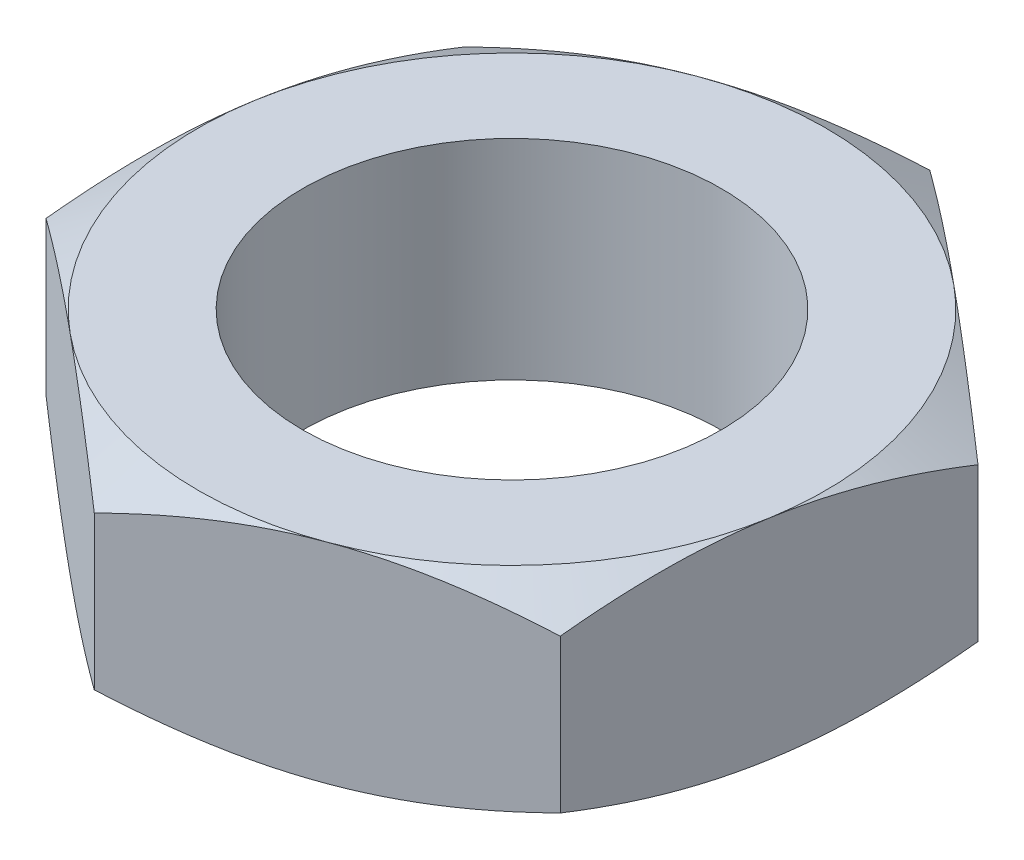
SolidWorks part; units mm, degrees
ref_plane "Front Plane" through (0, 0, 0) normal (0, 0, 1) x (1, 0, 0)
ref_plane "Top Plane" through (0, 0, 0) normal (0, 1, 0) x (1, 0, 0)
ref_plane "Right Plane" through (0, 0, 0) normal (1, 0, 0) x (0, 0, -1)
sketch "Sketch1" plane through (0, 0, 0) normal (0, 1, 0) x (1, 0, 0)
  line L1 (6.6732, -5.5198) -> (8.1169, 3.0193)
  line L2 (8.1169, 3.0193) -> (1.4437, 8.5391)
  line L3 (1.4437, 8.5391) -> (-6.6732, 5.5198)
  line L4 (-6.6732, 5.5198) -> (-8.1169, -3.0193)
  line L5 (-8.1169, -3.0193) -> (-1.4437, -8.5391)
  line L6 (-1.4437, -8.5391) -> (6.6732, -5.5198)
  circle A0 centre (0, 0) radius 7.5 construction
  dimension "D1" = 15
extrude "Boss-Extrude1" add sketch "Sketch1" along normal blind 5
sketch "Sketch7" plane through (0, 5, 0) normal (0, 1, 0) x (1, 0, 0)
  circle A0 centre (0, 0) radius 7.5
extrude "Cut-Extrude4" cut sketch "Sketch7" against normal blind 1 draft 60 flip side to cut
sketch "Sketch8" plane through (0, 0, 0) normal (0, -1, 0) x (1, 0, 0)
  circle A0 centre (0, 0) radius 7.5
extrude "Cut-Extrude5" cut sketch "Sketch8" against normal blind 1 draft 60 flip side to cut
sketch "Sketch9" plane through (0, 5, 0) normal (0, 1, 0) x (1, 0, 0)
  circle A0 centre (0, 0) radius 5
  dimension "D1" = 10
extrude "Cut-Extrude6" cut sketch "Sketch9" against normal blind 9
